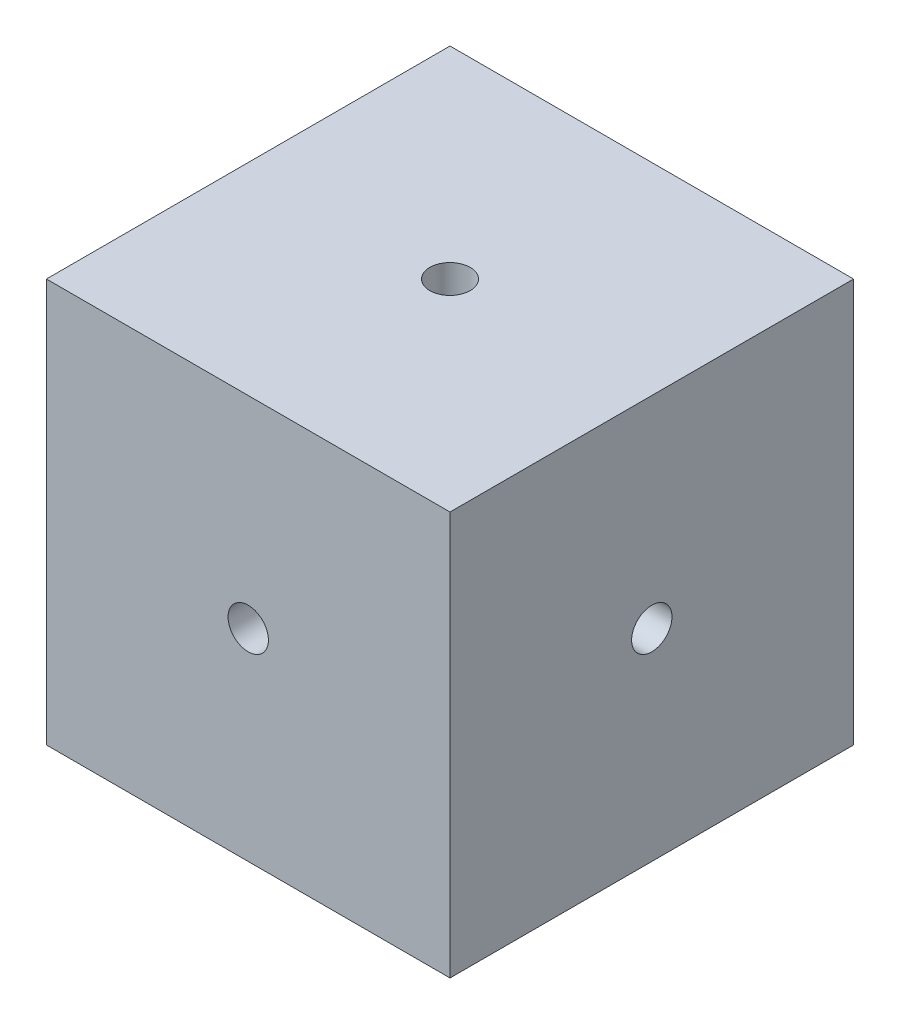
SolidWorks part; units mm, degrees
ref_plane "Front" through (0, 0, 0) normal (0, 0, 1) x (1, 0, 0)
ref_plane "Top" through (0, 0, 0) normal (0, 1, 0) x (1, 0, 0)
ref_plane "Right" through (0, 0, 0) normal (1, 0, 0) x (0, 0, -1)
sketch "Sketch1" plane through (0, 0, 0) normal (0, 1, 0) x (1, 0, 0)
  line L1 (-35, -35) -> (35, -35)
  line L2 (-35, -35) -> (-35, 35)
  line L3 (-35, 35) -> (35, 35)
  line L4 (35, -35) -> (35, 35)
  line L5 (-35, -35) -> (35, 35) construction
  line L6 (-35, 35) -> (35, -35) construction
  point P0 (0, 0)
  dimension "D1" = 70
extrude "Boss-Extrude1" add sketch "Sketch1" along normal mid plane 70
sketch "Sketch2" plane through (0, 35, 0) normal (0, 1, 0) x (1, 0, 0)
  circle A0 centre (0, 0) radius 3.5
  dimension "D1" = 7
extrude "Cut-Extrude1" cut sketch "Sketch2" against normal through all
sketch "Sketch3" plane through (0, 0, 35) normal (0, 0, 1) x (1, 0, 0)
  circle A0 centre (0, 0) radius 3.5
  dimension "D1" = 7
extrude "Cut-Extrude2" cut sketch "Sketch3" against normal through all
sketch "Sketch4" plane through (35, 0, 0) normal (1, 0, 0) x (0, 0, -1)
  circle A0 centre (0, 0) radius 3.5
  dimension "D1" = 7
extrude "Cut-Extrude3" cut sketch "Sketch4" against normal through all
sketch "Sketch5" plane through (0, -35, 0) normal (0, -1, 0) x (1, 0, 0)
  line L0 (7.3038, -10.5) -> (7.3038, -9)
  line L1 (-12.5, -10.5) -> (7.3038, -10.5)
  line L2 (-12.5, -10.5) -> (-12.5, -13.5)
  line L5 (7.3038, -9) -> (12.5, -12)
  line L8 (-12.5, -12) -> (12.5, -12) construction
  line L9 (7.3038, -15) -> (12.5, -12)
  line L10 (7.3038, -13.5) -> (7.3038, -15)
  line L11 (-12.5, -13.5) -> (7.3038, -13.5)
  point P8 (0, -12)
  dimension "D1" = 3
  dimension "D2" = 6
  dimension "D3" = 25
  dimension "D4" = 12
  dimension "D5" = 60
extrude "Cut-Extrude4" cut sketch "Sketch5" against normal blind 1
